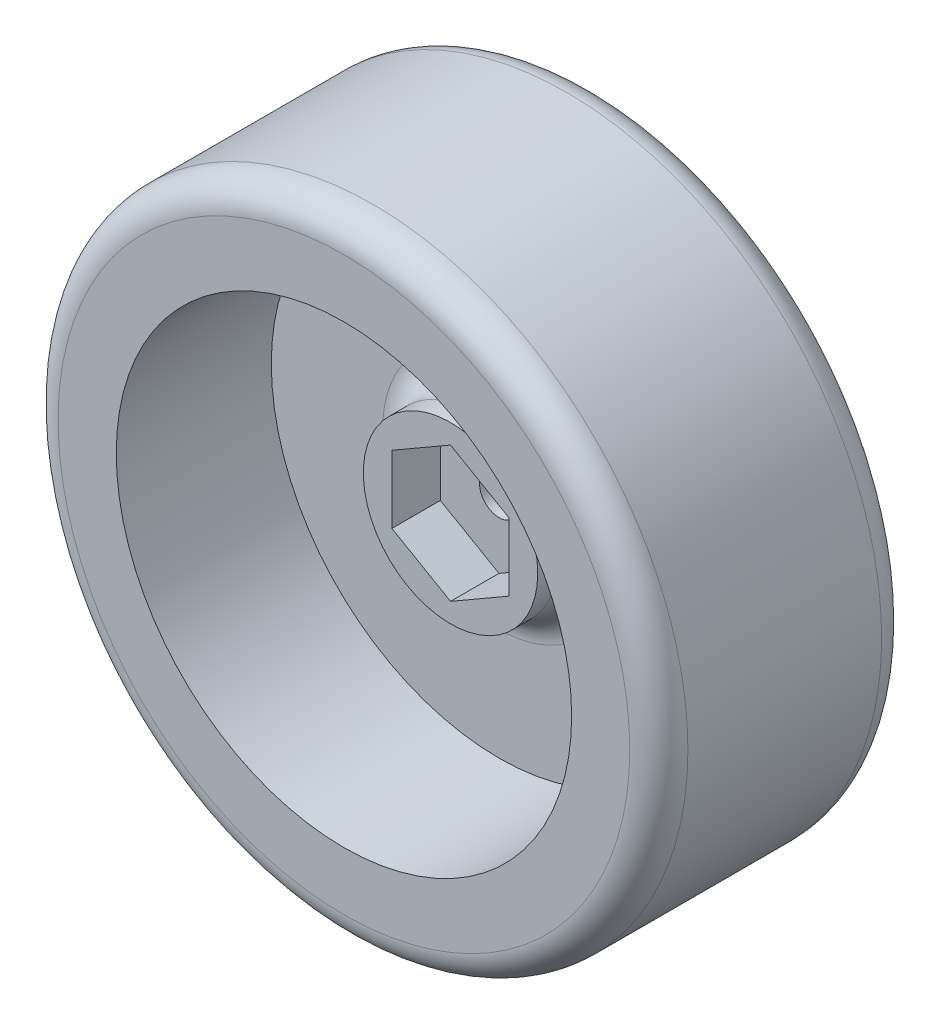
SolidWorks part; units mm, degrees
ref_plane "Front Plane" through (0, 0, 0) normal (0, 0, 1) x (1, 0, 0)
ref_plane "Top Plane" through (0, 0, 0) normal (0, 1, 0) x (1, 0, 0)
ref_plane "Right Plane" through (0, 0, 0) normal (1, 0, 0) x (0, 0, -1)
sketch "Sketch1" plane through (0, 0, 0) normal (0, 0, 1) x (1, 0, 0)
  circle A0 centre (0, 0) radius 32.5
  circle A1 centre (0, 0) radius 2
  dimension "D1" = 65
  dimension "D2" = 4
extrude "Boss-Extrude1" add sketch "Sketch1" along normal blind 26
fillet "Fillet1" radius 3 2 edges at (32.5, 0, 0) (32.5, 0, 26)
sketch "Sketch2" plane through (0, 0, 26) normal (0, 0, 1) x (1, 0, 0)
  circle A0 centre (0, 0) radius 23.5
  dimension "D1" = 47
extrude "Cut-Extrude1" cut sketch "Sketch2" against normal blind 16
sketch "Sketch3" plane through (0, 0, 10) normal (0, 0, 1) x (1, 0, 0)
  line L0 (0, 0) -> (50000, 0) construction
  line L1 (0, 0) -> (0, 50000) construction
  line L2 (-6.05, -3.493) -> (-6.05, 3.493)
  line L3 (6.05, -3.493) -> (6.05, 3.493)
  line L4 (-6.05, 3.493) -> (0, 6.9859)
  line L5 (-6.05, -3.493) -> (0, -6.9859)
  line L6 (6.05, -3.493) -> (0, -6.9859)
  line L7 (6.05, 3.493) -> (0, 6.9859)
  circle A0 centre (0, 0) radius 9
  point P10 (-6.05, 0)
  dimension "D4" = 18
  dimension "D1" = 12.1
  dimension "D2" = 12.1
  dimension "D3" = 12.1
extrude "Boss-Extrude2" add sketch "Sketch3" along normal blind 5
sketch "Sketch4" plane through (0, 0, 0) normal (0, 0, -1) x (-1, 0, 0)
  circle A0 centre (0, 0) radius 7.5
  dimension "D1" = 15
extrude "Cut-Extrude2" cut sketch "Sketch4" against normal blind 2
sketch "Sketch5" plane through (0, 0, 2) normal (0, 0, -1) x (-1, 0, 0)
  circle A0 centre (0, 0) radius 5
  dimension "D1" = 10
extrude "Cut-Extrude3" cut sketch "Sketch5" against normal blind 4
fillet "Fillet2" radius 3 1 edges at (9, 0, 10)
